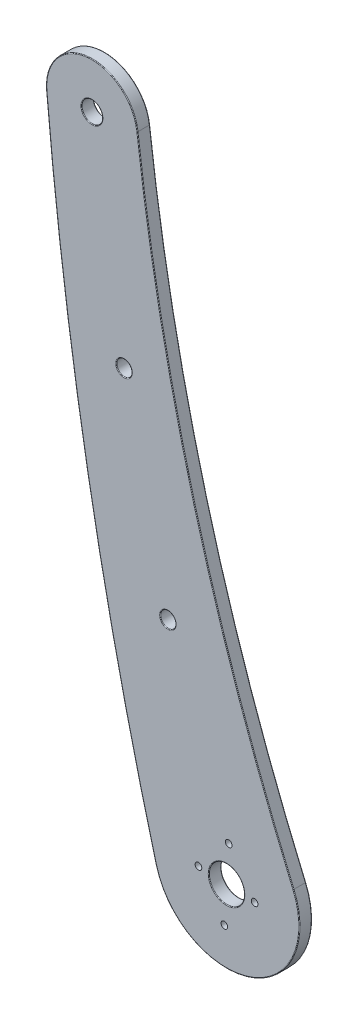
SolidWorks part; units mm, degrees
ref_plane "Front Plane" through (0, 0, 0) normal (0, 0, 1) x (1, 0, 0)
ref_plane "Top Plane" through (0, 0, 0) normal (0, 1, 0) x (1, 0, 0)
ref_plane "Right Plane" through (0, 0, 0) normal (1, 0, 0) x (0, 0, -1)
sketch "Sketch1" plane through (0, 0, 0) normal (0, 0, 1) x (1, 0, 0)
  line L0 (-20.22, 57.58) -> (-52.5327, 202.0095) construction
  line L1 (-20.22, 57.58) -> (-52.5327, 202.0095) construction
  circle A0 centre (-20.22, 57.58) radius 17.5 construction
  circle A1 centre (-52.5327, 202.0095) radius 11 construction
  circle A2 centre (-20.22, 57.58) radius 17.5 construction
  circle A3 centre (-52.5327, 202.0095) radius 11 construction
  circle A4 centre (-52.5327, 202.0095) radius 2.5
  circle A7 centre (-20.22, 57.58) radius 4.25
  arc A8 (-41.6109, 203.3189) -> (-4.1554, 64.521) centre (454.8343, 262.8351) ccw
  arc A9 (-52.5327, 202.0095) -> (-20.22, 57.58) centre (691.9588, 292.7424) ccw construction
  arc A10 (-63.4903, 201.0453) -> (-37.1095, 52.998) centre (783.238, 275.5513) ccw
  arc A11 (-63.4903, 201.0453) -> (-41.6109, 203.3189) centre (-52.5327, 202.0095) cw
  arc A12 (-37.1095, 52.998) -> (-4.1554, 64.521) centre (-20.22, 57.58) ccw
  point P17 (-44.8327, 152.606)
  point P18 (-34.3062, 105.5548)
  point P19 (-44.8327, 152.606)
  point P21 (-52.5327, 202.0095)
  dimension "D1" = 5
  dimension "D2" = 8.5
  dimension "D3" = 850
  dimension "D4" = 500
  dimension "D5" = 750
  dimension "D6" = 50
  dimension "D7" = 50
extrude "Boss-Extrude1" add sketch "Sketch1" against normal blind 3
hole_wizard "M3.5 Clearance Hole2" positions "Sketch3" profile "Sketch4" hole size "M3.5" standard "ISO" end condition through all
sketch "Sketch3" plane through (0, 0, -3) normal (0, 0, -1) x (-1, 0, 0)
  point P0 (44.8327, 152.606)
  point P3 (34.3062, 105.5548)
sketch "Sketch4" plane through (-44.8327, 152.606, -3) normal (1, 0, 0) x (0, 1, 0)
  line L0 (0, 0) -> (0, 3)
  line L1 (0, 3) -> (1.85, 3)
  line L2 (1.85, 3) -> (1.85, 0)
  line L5 (1.85, 0) -> (0, 0)
  line L11 (0, -6.35) -> (0, 107.95) construction
  dimension "Thru Hole Dia." = 3.7
  dimension "Thru Hole Depth" = 3
fillet "Fillet1" radius 0.15 16 edges at (-27.8977, 132.5667, 0) (-14.4438, 41.0608, 0) (-53.5804, 126.4371, 0) (-53.6696, 212.9506, 0) (-50.0327, 202.0095, 0) (-15.97, 57.58, 0) (-36.1562, 105.5548, 0) (-46.6827, 152.606, 0) (-53.5804, 126.4371, -3) (-14.4438, 41.0608, -3) (-27.8977, 132.5667, -3) (-53.6696, 212.9506, -3) (-50.0327, 202.0095, -3) (-15.97, 57.58, -3) (-36.1562, 105.5548, -3) (-46.6827, 152.606, -3)
sketch "Sketch5" plane through (0, 0, -3) normal (0, 0, -1) x (-1, 0, 0)
  line L0 (20.2472, 57.1279) -> (20.22, 57.58) construction
  line L1 (20.22, 57.58) -> (26.9579, 57.9847) construction
  line L2 (22.102, 61.9005) -> (20.22, 57.58) construction
  line L3 (20.22, 57.58) -> (20.7446, 48.8457) construction
  line L4 (20.7446, 48.8457) -> (21.161, 57.1279) construction
  circle A0 centre (26.9579, 57.9847) radius 0.8
  circle A1 centre (20.7446, 48.8457) radius 0.8
  circle A2 centre (13.4821, 57.1753) radius 0.8
  circle A3 centre (19.6954, 66.3143) radius 0.8
extrude "Cut-Extrude1" cut sketch "Sketch5" against normal blind 10
